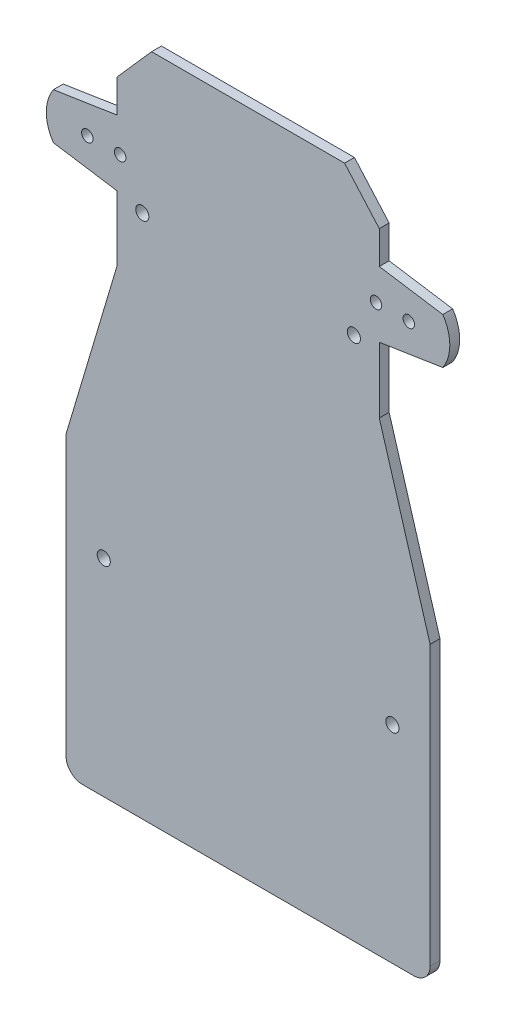
SolidWorks part; units mm, degrees
ref_plane "前视基准面" through (0, 0, 0) normal (0, 0, 1) x (1, 0, 0)
ref_plane "上视基准面" through (0, 0, 0) normal (0, 1, 0) x (1, 0, 0)
ref_plane "右视基准面" through (0, 0, 0) normal (1, 0, 0) x (0, 0, -1)
sketch "草图1" plane through (0, 0, 0) normal (0, 0, 1) x (1, 0, 0)
  line L0 (0, 0) -> (0, 11.0936) construction
  line L1 (-29.417, 204) -> (29.417, 204)
  line L2 (-29.417, 204) -> (-40, 192)
  line L3 (-40, 192) -> (-40, 182)
  line L4 (-40, 182) -> (-59.3562, 179)
  line L6 (-59.3562, 165) -> (-40, 162)
  line L7 (-40, 162) -> (-40, 142)
  line L8 (-40, 142) -> (-55.5, 90)
  line L9 (-55.5, 90) -> (-55.5, 0)
  line L10 (55.5, 90) -> (55.5, 0)
  line L11 (40, 142) -> (55.5, 90)
  line L12 (40, 162) -> (40, 142)
  line L13 (59.3562, 165) -> (40, 162)
  line L15 (40, 182) -> (59.3562, 179)
  line L16 (40, 192) -> (40, 182)
  line L17 (29.417, 204) -> (40, 192)
  line L18 (-55.5, 0) -> (55.5, 0)
  line L19 (-49, 172) -> (49, 172) construction
  line L20 (-40, 182) -> (-40, 162) construction
  arc A0 (-59.3562, 179) -> (-59.3562, 165) centre (-49, 172) ccw
  arc A1 (59.3562, 165) -> (59.3562, 179) centre (49, 172) ccw
  circle A2 centre (-49, 172) radius 1.75
  circle A3 centre (49, 172) radius 1.75
  circle A4 centre (39, 172) radius 1.75
  circle A5 centre (-39, 172) radius 1.75
  point P3 (-40, 187)
  point P23 (-40, 172)
  dimension "D10" = 12.5
  dimension "D13" = 3.5
  dimension "D1" = 111
  dimension "D2" = 90
  dimension "D3" = 80
  dimension "D4" = 142
  dimension "D5" = 14
  dimension "D6" = 10
  dimension "D7" = 20
  dimension "D8" = 20
  dimension "D9" = 98
  dimension "D11" = 16
  dimension "D12" = 12
  dimension "D14" = 10
  dimension "D15" = 10
extrude "凸台-拉伸1" add sketch "草图1" along normal blind 3
fillet "圆角1" radius 5 2 edges at (55.5, 0, 1.5) (-55.5, 0, 1.5)
sketch "草图2" plane through (0, 0, 3) normal (0, 0, 1) x (1, 0, 0)
  line L0 (-32.25, 160) -> (32.25, 160)
  line L1 (-44, 63) -> (44, 63)
hole_wizard "大小mm 暗销孔1" positions "草图3" profile "草图4" hole size "Ø4.0" standard "ISO" end condition through all
sketch "草图3" plane through (0, 0, 0) normal (0, 0, -1) x (-1, 0, 0)
  point P0 (-32.25, 160)
  point P3 (32.25, 160)
  point P10 (44, 63)
  point P13 (-44, 63)
sketch "草图4" plane through (32.25, 160, 0) normal (1, 0, 0) x (0, 1, 0)
  line L0 (0, 0) -> (0, 3)
  line L1 (0, 3) -> (2, 3)
  line L2 (2, 3) -> (2, 0)
  line L5 (2, 0) -> (0, 0)
  line L11 (0, -6.35) -> (0, 107.95) construction
  dimension "通孔孔直径" = 4
  dimension "通孔孔深度" = 3
